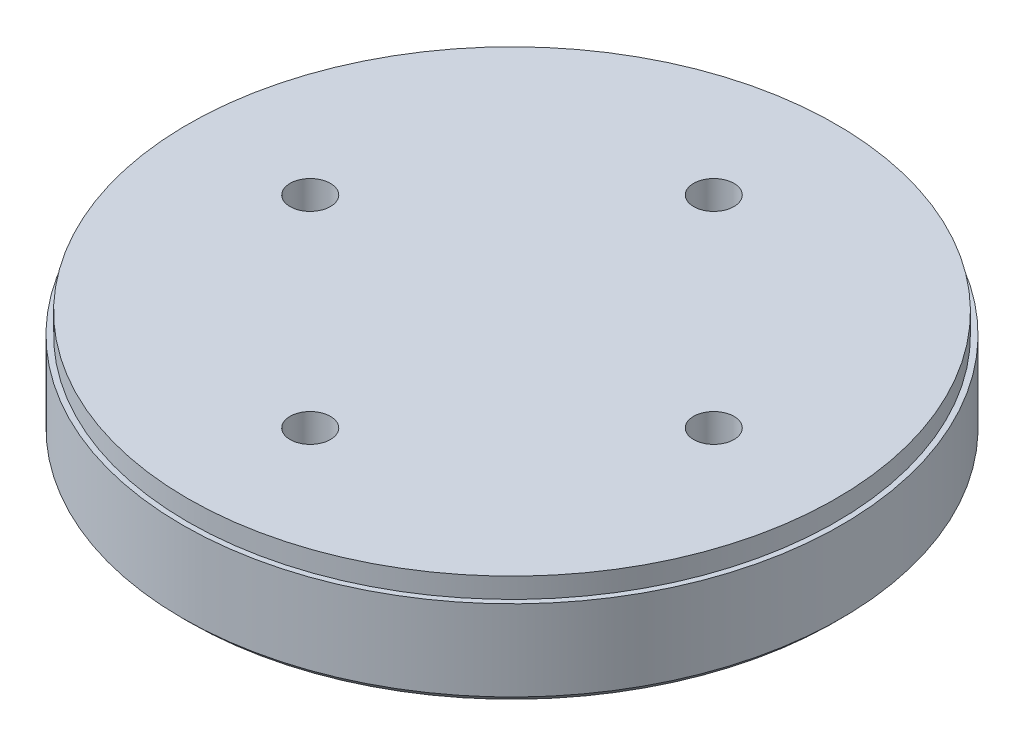
SolidWorks part; units mm, degrees
material "ABS"
ref_plane "Plan de face" through (0, 0, 0) normal (0, 0, 1) x (1, 0, 0)
ref_plane "Plan de dessus" through (0, 0, 0) normal (0, 1, 0) x (1, 0, 0)
ref_plane "Plan de droite" through (0, 0, 0) normal (1, 0, 0) x (0, 0, -1)
sketch "Esquisse1" plane through (0, 0, 0) normal (0, 1, 0) x (1, 0, 0)
  circle A0 centre (0, 0) radius 24.5
  circle A1 centre (0, 0) radius 15 construction
  circle A2 centre (0, 15) radius 1.5
  circle A3 centre (15, 0) radius 1.5
  circle A4 centre (0, -15) radius 1.5
  circle A5 centre (-15, 0) radius 1.5
  point P14 (0, 0)
  dimension "D1" = 49
  dimension "D2" = 30
  dimension "D3" = 3
  dimension "D4" = 4
extrude "Boss.-Extru.1" add sketch "Esquisse1" along normal blind 8
sketch "Esquisse2" plane through (0, 8, 0) normal (0, 1, 0) x (1, 0, 0)
  circle A2 centre (0, 0) radius 24.1
  circle A3 centre (0, 0) radius 24.1
  dimension "D1" = 0.4
extrude "Enlèv. mat.-Extru.1" cut sketch "Esquisse2" against normal blind 1.5 flip side to cut
chamfer "Chanfrein1" distance 0.5 angle 45 1 edges at (0, 0, 24.5)
